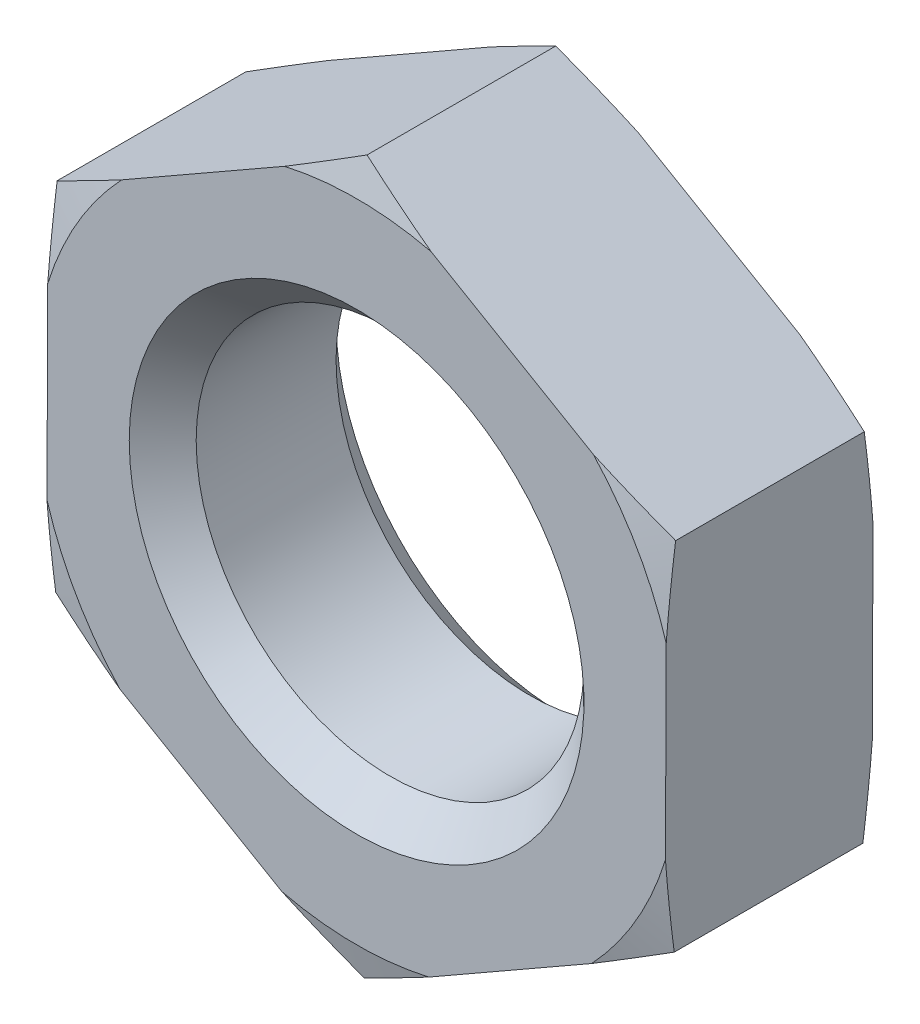
SolidWorks part; units mm, degrees
material "04级"
ref_plane "基准面1" through (0, 0, 0) normal (0, 0, 1) x (1, 0, 0)
ref_plane "基准面2" through (0, 0, 0) normal (0, 1, 0) x (1, 0, 0)
ref_plane "基准面3" through (0, 0, 0) normal (1, 0, 0) x (0, 0, -1)
sketch "尺寸草图" plane through (0, 0, 0) normal (0, 0, 1) x (1, 0, 0)
  line L0 (0, 0) -> (24.1005, 0)
  line L1 (0, 0) -> (6.75, 0)
  line L2 (46.8781, 0) -> (55.7781, 0)
  line L3 (-5.7143, 0) -> (0, 0)
  point P3 (6, 0)
  point P4 (2.5, 0)
  point P5 (11.05, 0)
  point P6 (3.2, 0)
  point P7 (7.3, 0)
  point P8 (10, 0)
  dimension "D1" = 5.7143
  dimension "D" = 6
  dimension "P" = 2.5
  dimension "e" = 11.05
  dimension "m" = 3.2
  dimension "mw" = 7.3
  dimension "s" = 10
  dimension "da" = 6.75
  dimension "dw" = 8.9
sketch "草图1" plane through (0, 0, 0) normal (0, 0, 1) x (1, 0, 0)
  line L0 (-26.8088, 0) -> (37.1748, 0) construction
  line L1 (0, 25.0215) -> (0, -25.0215) construction
  line L3 (0.0217, 5.525) -> (-4.7739, 2.7813)
  line L4 (-4.7739, 2.7813) -> (-4.7956, -2.7437)
  line L5 (-4.7956, -2.7437) -> (-0.0217, -5.525)
  line L6 (-0.0217, -5.525) -> (4.7739, -2.7813)
  line L7 (4.7739, -2.7813) -> (4.7956, 2.7437)
  line L8 (4.7956, 2.7437) -> (0.0217, 5.525)
  circle A0 centre (0, 0) radius 4.7848 construction
  circle A1 centre (0, 0) radius 3
  dimension "D" = 6
  dimension "e" = 11.05
extrude "基体-拉伸" add sketch "草图1" along normal blind 3.2
cosmetic thread "装饰螺纹线1"
chamfer "倒角1" distance 0.5179 angle 45 2 edges at (3, 0, 0) (3, 0, 3.2)
sketch "草图2" plane through (0, 0, 0) normal (0, 0, -1) x (-1, 0, 0)
  circle A0 centre (0, 0) radius 5
  circle A1 centre (0, 0) radius 3 construction
  dimension "s" = 10
extrude "切除-拉伸1" cut sketch "草图2" against normal through all draft 75 flip side to cut
sketch "草图3" plane through (0, 0, 3.2) normal (0, 0, 1) x (1, 0, 0)
  circle A0 centre (0, 0) radius 5
  dimension "D1" = 10
extrude "切除-拉伸2" cut sketch "草图3" against normal through all draft 75 flip side to cut
equation "\"e@草图1\" = \"e@尺寸草图\""
equation "\"D1@尺寸草图\" = \"D@尺寸草图\" / 1.05"
equation "\"D@草图1\" = \"D@尺寸草图\""
equation "\"m@基体-拉伸\" = \"m@尺寸草图\""
equation "\"D1@草图3\" = \"s@尺寸草图\""
equation "\"s@草图2\" = \"s@尺寸草图\""
equation "\"D2@装饰螺纹线1\" = 1.05 * \"D1@尺寸草图\""
equation "\"D1@倒角1\" =  ( \"da@尺寸草图\" - \"D1@尺寸草图\" )  / 2"
